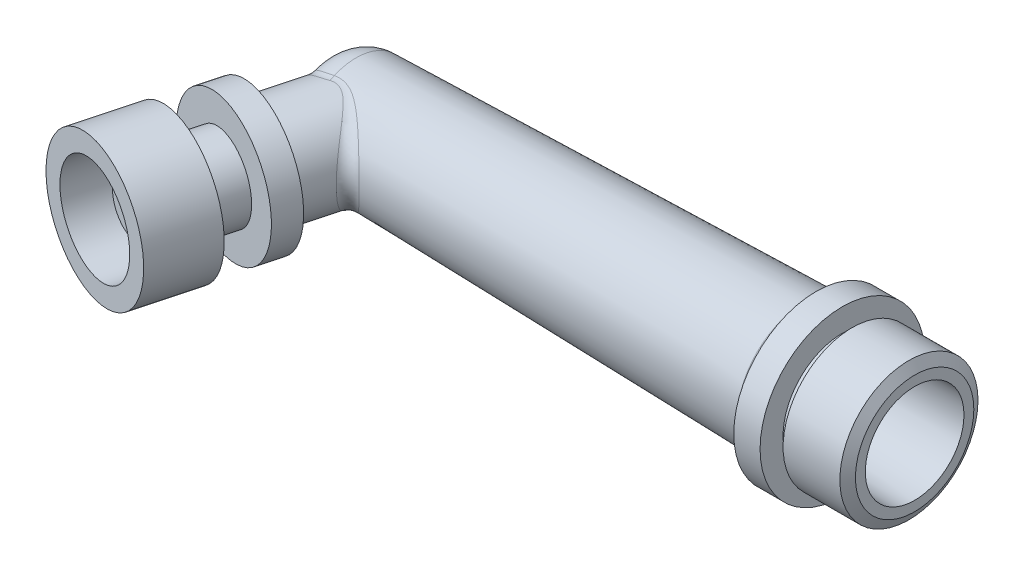
SolidWorks part; units mm, degrees
ref_plane "Front Plane" through (0, 0, 0) normal (0, 0, 1) x (1, 0, 0)
ref_plane "Top Plane" through (0, 0, 0) normal (0, 1, 0) x (1, 0, 0)
ref_plane "Right Plane" through (0, 0, 0) normal (1, 0, 0) x (0, 0, -1)
sketch "Sketch1" plane through (0, 0, 0) normal (0, 1, 0) x (1, 0, 0)
  line L0 (0, 0) -> (-83, 0) construction
  line L1 (-83, 0) -> (-88.3472, -19.9559) construction
  line L2 (-88.3472, -19.9559) -> (-94.6577, -43.5072) construction
  line L3 (-83, 0) -> (-77.1904, 21.6817) construction
  line L4 (-83, 0) -> (-83, 32.3395) construction
  line L6 (-83, 5.5) -> (0, 7.5)
  line L9 (-0.866, 10.5) -> (-9.5, 10.5)
  line L10 (-15, 11.9524) -> (-15, 12.5)
  line L11 (-15, 12.5) -> (-11, 12.5)
  line L12 (-11, 12.5) -> (-11, 9)
  line L13 (-11, 9) -> (-9.5, 9)
  line L14 (-9.5, 9) -> (-9.5, 10.5)
  line L21 (-0.866, 10.5) -> (0, 9)
  line L23 (-16.9518, 9.953) -> (-84.9205, 8.3152)
  line L26 (-89.8, 0) -> (-89.8, 3.3281)
  line L28 (0, 7.5) -> (0, 9)
  line L30 (-88.5, 0) -> (-89.8, 0)
  arc A0 (-83, 5.5) -> (-88.5, 0) centre (-83, 0) ccw
  arc A1 (-15, 11.9524) -> (-16.9518, 9.953) centre (-17, 11.9524) cw
  arc A3 (-89.8, 3.3281) -> (-84.9205, 8.3152) centre (-84.8, 3.3166) cw
  point P10 (-83, 5.5)
  point P11 (-83, -5.5)
  point P14 (0, 0)
  point P15 (0, 0)
  point P22 (0, 0)
  point P23 (0, 0)
  point P24 (0, 0)
  point P37 (-15, 10)
  point P49 (-89.8114, 0)
  dimension "D2" = 15
  dimension "D11" = 2
  dimension "D12" = 5
  dimension "D3" = 5.5
  dimension "D1" = 83
  dimension "D4" = 7.5
  dimension "D5" = 73.62
  dimension "D6" = 6.8
  dimension "D7" = 10
  dimension "D8" = 12.5
  dimension "D9" = 9
  dimension "D10" = 1.5
revolve "Revolve1" add sketch "Sketch1" angle 360 about L0
sketch "Sketch2" plane through (0, 0, 0) normal (0, 1, 0) x (1, 0, 0)
  line L0 (-86.6235, -13.523) -> (-96.5242, -10.8701)
  line L1 (-78.7359, 15.9138) -> (-92.1909, -34.301) construction
  line L2 (-83, 0) -> (-83, 24.4488) construction
  line L3 (-94.4989, -27.4595) -> (-90.6352, -28.4948)
  line L4 (-86.6235, -13.523) -> (-93.8679, -11.5818)
  line L5 (-99.0443, -30.9003) -> (-101.9421, -30.1239)
  line L6 (-101.9421, -30.1239) -> (-99.3539, -20.4646)
  line L7 (-99.0443, -30.9003) -> (-101.9421, -30.1239)
  line L8 (-99.3539, -20.4646) -> (-95.0072, -21.6293)
  line L9 (-95.0072, -21.6293) -> (-93.4543, -15.8338)
  line L10 (-93.4543, -15.8338) -> (-97.5595, -14.7338)
  line L11 (-97.5595, -14.7338) -> (-96.5242, -10.8701)
  line L13 (-94.4989, -27.4595) -> (-93.7224, -24.5618)
  line L15 (-99.0443, -30.9003) -> (-97.1031, -23.6559)
  line L16 (-93.7224, -24.5618) -> (-97.1031, -23.6559)
  line L20 (-86.6235, -13.523) -> (-90.6352, -28.4948)
  point P5 (-83, 0)
  dimension "D2" = 15
  dimension "D3" = 4.5
  dimension "D4" = 7.5
  dimension "D5" = 3.5
  dimension "D6" = 34
  dimension "D7" = 3
  dimension "D8" = 10
  dimension "D9" = 6
  dimension "D10" = 6
  dimension "D11" = 10.25
  dimension "D14" = 4
  dimension "20" = 20
revolve "Revolve2" add sketch "Sketch2" angle 360 about L1
ref_plane "Plane1" through (-9.1834, 0, 34.273) normal (0.2588, 0, -0.9659) x (-0.9659, 0, -0.2588)
sketch "Sketch3" plane through (-9.1834, 0, 34.273) normal (0.2588, 0, -0.9659) x (-0.9659, 0, -0.2588)
  circle A0 centre (80.1718, 0) radius 7.5
extrude "Boss-Extrude1" add sketch "Sketch3" along normal up to body
ref_plane "Plane2" through (-13.1951, 0, 49.2448) normal (-0.2588, 0, 0.9659) x (0.9659, 0, 0.2588)
sketch "Sketch4" plane through (-13.1951, 0, 49.2448) normal (-0.2588, 0, 0.9659) x (0.9659, 0, 0.2588)
  circle A0 centre (-80.1718, 0) radius 2.5
extrude "Cut-Extrude1" cut sketch "Sketch4" against normal up to next
fillet "Fillet1" radius 2 8 edges at (-89.8, 2.6687, -1.9886) (-89.8, -2.6687, -1.9886) (-77.606, 1.3319, 8.3863) (-87.7793, 6.5014, 3.3897) (-89.8, 2.4608, -1.9956) (-89.7897, 0.0615, -3.6374) (-89.8, -2.4608, -1.9956) (-88.3746, -6.0775, 3.0783)
